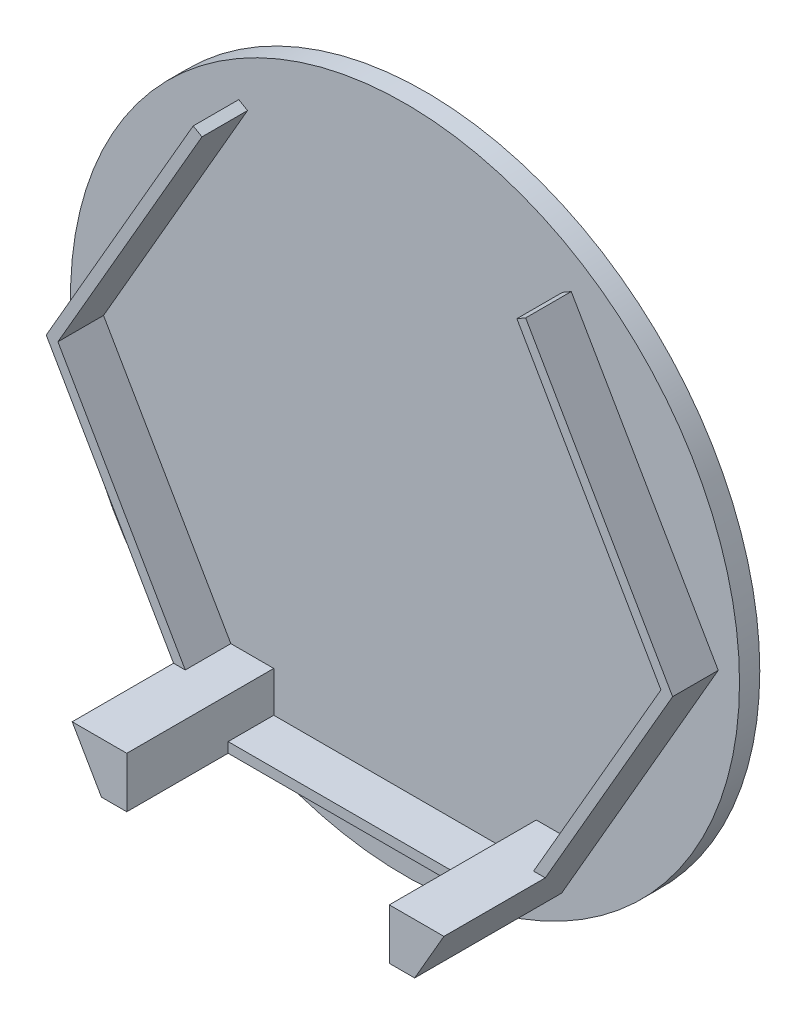
SolidWorks part; units mm, degrees
ref_plane "Front Plane" through (0, 0, 0) normal (0, 0, 1) x (1, 0, 0)
ref_plane "Top Plane" through (0, 0, 0) normal (0, 1, 0) x (1, 0, 0)
ref_plane "Right Plane" through (0, 0, 0) normal (1, 0, 0) x (0, 0, -1)
sketch "Sketch1" plane through (0, 0, 0) normal (0, 0, 1) x (1, 0, 0)
  circle A0 centre (0, 0) radius 33
extrude "Boss-Extrude1" add sketch "Sketch1" along normal blind 2
sketch "Sketch3" plane through (0, 0, 2) normal (0, 0, 1) x (1, 0, 0)
  line L0 (-15.534, 24.6147) -> (-29.7453, 0)
  line L1 (30.9, 0) -> (16.4, 25.1147)
  line L2 (-29.7453, 0) -> (-17.1821, -21.7602)
  line L3 (-16.4, 25.1147) -> (-30.9, 0)
  line L4 (-30.9, 0) -> (-15.45, -26.7602)
  line L5 (-15.45, -26.7602) -> (15.45, -26.7602)
  line L6 (15.45, -26.7602) -> (30.9, 0)
  line L7 (15.45, 26.7602) -> (-15.45, 26.7602) [skipped]
  line L8 (-12.95, -25.7602) -> (12.95, -25.7602)
  line L9 (17.1821, -21.7602) -> (29.7453, 0)
  line L10 (29.7453, 0) -> (15.534, 24.6147)
  line L11 (-16.4, 25.1147) -> (-15.534, 24.6147)
  line L12 (15.534, 24.6147) -> (16.4, 25.1147)
  line L14 (-12.95, -25.7602) -> (-12.95, -21.7602)
  line L15 (-12.95, -21.7602) -> (-17.1821, -21.7602)
  line L16 (12.95, -25.7602) -> (12.95, -21.7602)
  line L17 (-29.7453, 0) -> (-14.8726, -25.7602) construction
  line L18 (-14.8726, -25.7602) -> (14.8726, -25.7602) construction
  line L19 (-15.45, -26.7602) -> (15.45, -26.7602) construction
  line L20 (-12.95, -26.7602) -> (15.45, -26.7602) [skipped]
  line L21 (12.95, -21.7602) -> (17.1821, -21.7602)
  line L23 (14.8726, -25.7602) -> (29.7453, 0) construction
  dimension "D1" = 1
extrude "Boss-Extrude2" add sketch "Sketch3" along normal blind 4.5
sketch "Sketch4" plane through (0, 0, 6.5) normal (0, 0, 1) x (1, 0, 0)
  line L0 (-12.95, -21.7602) -> (-18.3368, -21.7602)
  line L1 (-30.9, 0) -> (-15.45, -26.7602) construction
  line L2 (-18.3368, -21.7602) -> (-15.45, -26.7602)
  line L3 (-15.45, -26.7602) -> (-12.95, -26.7602)
  line L4 (-15.45, -26.7602) -> (15.45, -26.7602) construction
  line L5 (-12.95, -26.7602) -> (-12.95, -21.7602)
  line L6 (12.95, -21.7602) -> (12.95, -26.7602)
  line L7 (-15.45, -26.7602) -> (15.45, -26.7602) construction
  line L8 (12.95, -26.7602) -> (15.45, -26.7602)
  line L9 (15.45, -26.7602) -> (18.3368, -21.7602)
  line L10 (15.45, -26.7602) -> (30.9, 0) construction
  line L11 (18.3368, -21.7602) -> (12.95, -21.7602)
extrude "Boss-Extrude3" add sketch "Sketch4" along normal blind 10
